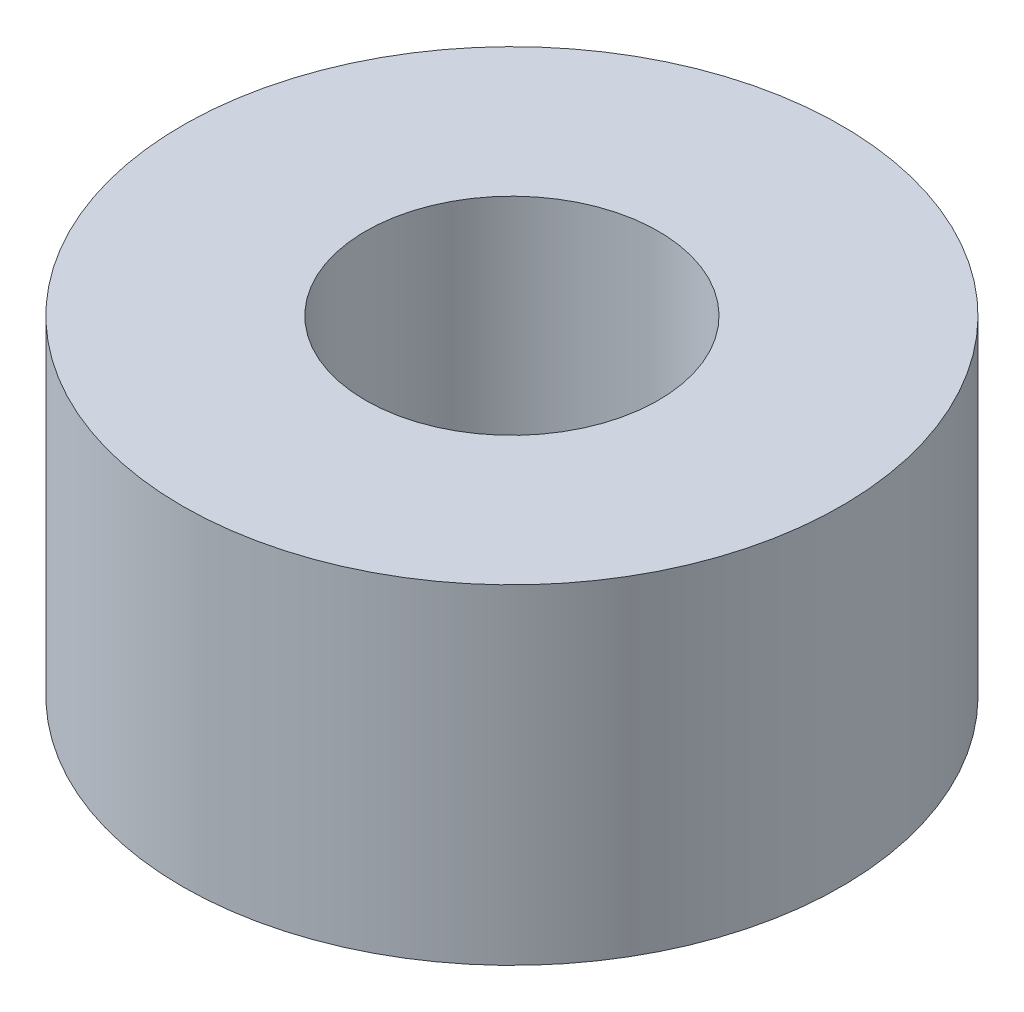
SolidWorks part; units mm, degrees
material "PTFE (general)"
ref_plane "Front Plane" through (0, 0, 0) normal (0, 0, 1) x (1, 0, 0)
ref_plane "Top Plane" through (0, 0, 0) normal (0, 1, 0) x (1, 0, 0)
ref_plane "Right Plane" through (0, 0, 0) normal (1, 0, 0) x (0, 0, -1)
sketch "Sketch2" plane through (0, 0, 0) normal (0, 1, 0) x (1, 0, 0)
  circle A0 centre (0, 0) radius 2
  circle A1 centre (0, 0) radius 4.5
extrude "Boss-Extrude1" add sketch "Sketch2" along normal blind 4.5
